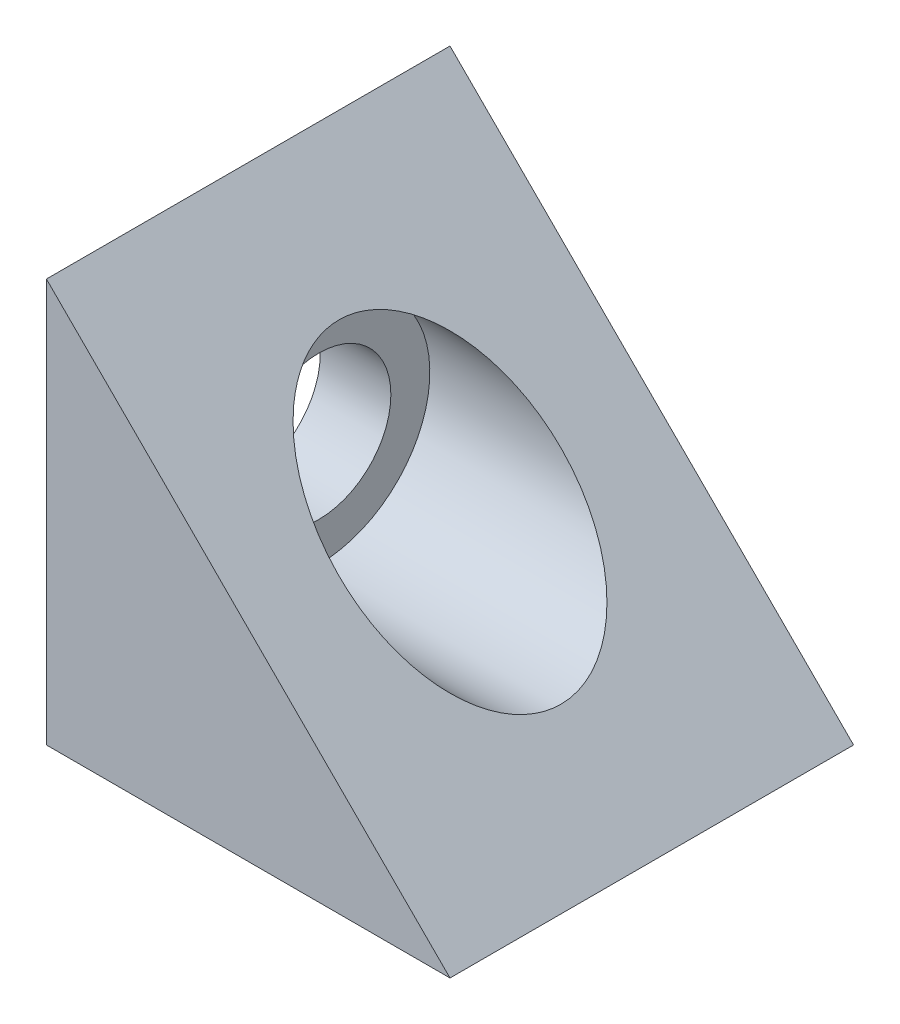
SolidWorks part; units mm, degrees
ref_plane "Front Plane" through (0, 0, 0) normal (0, 0, 1) x (1, 0, 0)
ref_plane "Top Plane" through (0, 0, 0) normal (0, 1, 0) x (1, 0, 0)
ref_plane "Right Plane" through (0, 0, 0) normal (1, 0, 0) x (0, 0, -1)
sketch "Sketch1" plane through (0, 0, 0) normal (0, 0, 1) x (1, 0, 0)
  line L0 (0, 0) -> (0, 20)
  line L1 (0, 20) -> (20, 0)
  line L2 (20, 0) -> (0, 0)
  dimension "D1" = 20
  dimension "D2" = 20
extrude "Boss-Extrude1" add sketch "Sketch1" against normal mid plane 20
ref_plane "Plane1" through (20, 0, 0) normal (1, 0, 0) x (0, 0, -1)
sketch "Sketch2" plane through (20, 0, 0) normal (1, 0, 0) x (0, 0, -1)
  line L1 (-10, 0) -> (10, 0) construction
  line L2 (-10, 0) -> (-10, 20) construction
  line L3 (-10, 20) -> (10, 20) construction
  line L4 (10, 0) -> (10, 20) construction
  circle A0 centre (0, 10) radius 3.57
  dimension "D3" = 7.14
  dimension "D1" = 20
  dimension "D2" = 20
  dimension "D4" = 10
extrude "Cut-Extrude1" cut sketch "Sketch2" against normal through all
sketch "Sketch3" plane through (20, 0, 0) normal (1, 0, 0) x (0, 0, -1)
  circle A0 centre (0, 10) radius 5.5
  dimension "D1" = 11
extrude "Cut-Extrude2" cut sketch "Sketch3" against normal offset from surface (16.5 mm away) 3.5 up to face at (0, 10, -3.57)
